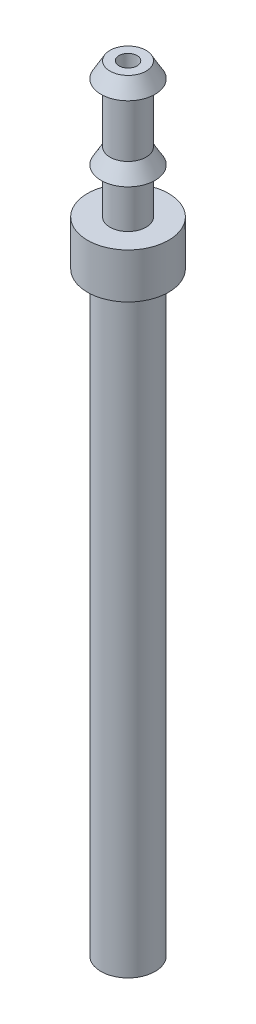
SolidWorks part; units mm, degrees
ref_plane "Спереди" through (0, 0, 0) normal (0, 0, 1) x (1, 0, 0)
ref_plane "Сверху" through (0, 0, 0) normal (0, 1, 0) x (1, 0, 0)
ref_plane "Справа" through (0, 0, 0) normal (1, 0, 0) x (0, 0, -1)
sketch "Эскиз1" plane through (0, 0, 0) normal (0, 0, 1) x (1, 0, 0)
  line L0 (0, 0) -> (0, -66) construction
  line L1 (-1, -66) -> (-3, -66)
  line L2 (-3, -66) -> (-3, 0)
  line L3 (-3, 0) -> (-4.5, 0)
  line L4 (-4.5, 0) -> (-4.5, 5)
  line L5 (-4.5, 5) -> (-2, 5)
  line L6 (-2, 5) -> (-2, 10)
  line L7 (-2, 10) -> (-3, 10)
  line L8 (-3, 10) -> (-2, 11.7321)
  line L9 (-2, 11.7321) -> (-2, 18.2679)
  line L10 (-2, 18.2679) -> (-3, 18.2679)
  line L11 (-3, 18.2679) -> (-2, 20)
  line L13 (-2, 20) -> (-1, 20)
  line L14 (-1, 20) -> (-1, -66)
  line L15 (0, 0) -> (0, 20) construction
  line L16 (-1, 20) -> (0, 20) construction
  line L17 (0, -66) -> (-1, -66) construction
  line L18 (-3, 18.2679) -> (-3, 10) construction
  dimension "D1" = 2
  dimension "D2" = 6
  dimension "D3" = 5
  dimension "D4" = 4
  dimension "D5" = 60
  dimension "D6" = 60
  dimension "D7" = 15
  dimension "D8" = 66
  dimension "D9" = 9
  dimension "D10" = 10
  dimension "D11" = 6
  dimension "D12" = 1
  dimension "D13" = 4
revolve "Повернуть1" add sketch "Эскиз1" angle 360 about L15
